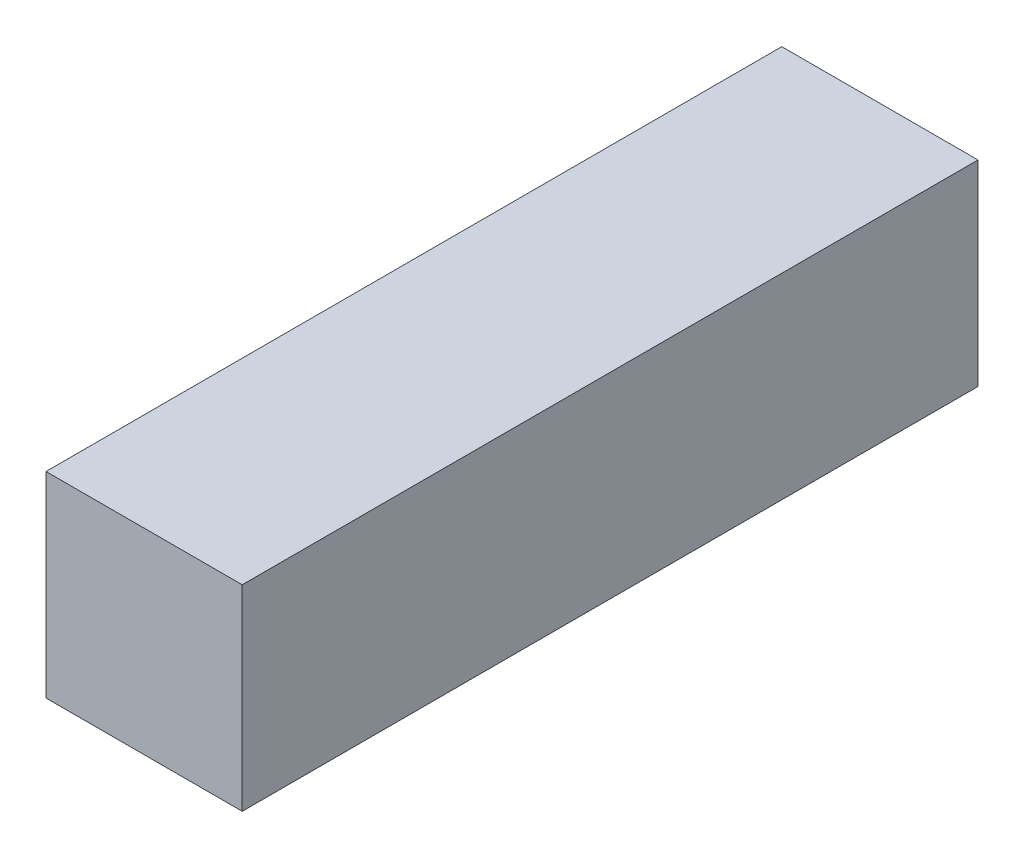
SolidWorks part; units mm, degrees
ref_plane "Front Plane" through (0, 0, 0) normal (0, 0, 1) x (1, 0, 0)
ref_plane "Top Plane" through (0, 0, 0) normal (0, 1, 0) x (1, 0, 0)
ref_plane "Right Plane" through (0, 0, 0) normal (1, 0, 0) x (0, 0, -1)
sketch "Sketch7" plane through (0, 0, 0) normal (0, 0, 1) x (1, 0, 0)
  line L1 (-10.16, -10.16) -> (10.16, -10.16)
  line L2 (-10.16, -10.16) -> (-10.16, 10.16)
  line L3 (-10.16, 10.16) -> (10.16, 10.16)
  line L4 (10.16, -10.16) -> (10.16, 10.16)
  line L5 (-10.16, -10.16) -> (10.16, 10.16) construction
  line L6 (-10.16, 10.16) -> (10.16, -10.16) construction
  point P0 (0, 0)
  dimension "D1" = 20.32
extrude "Boss-Extrude3" add sketch "Sketch7" along normal mid plane 76.2
